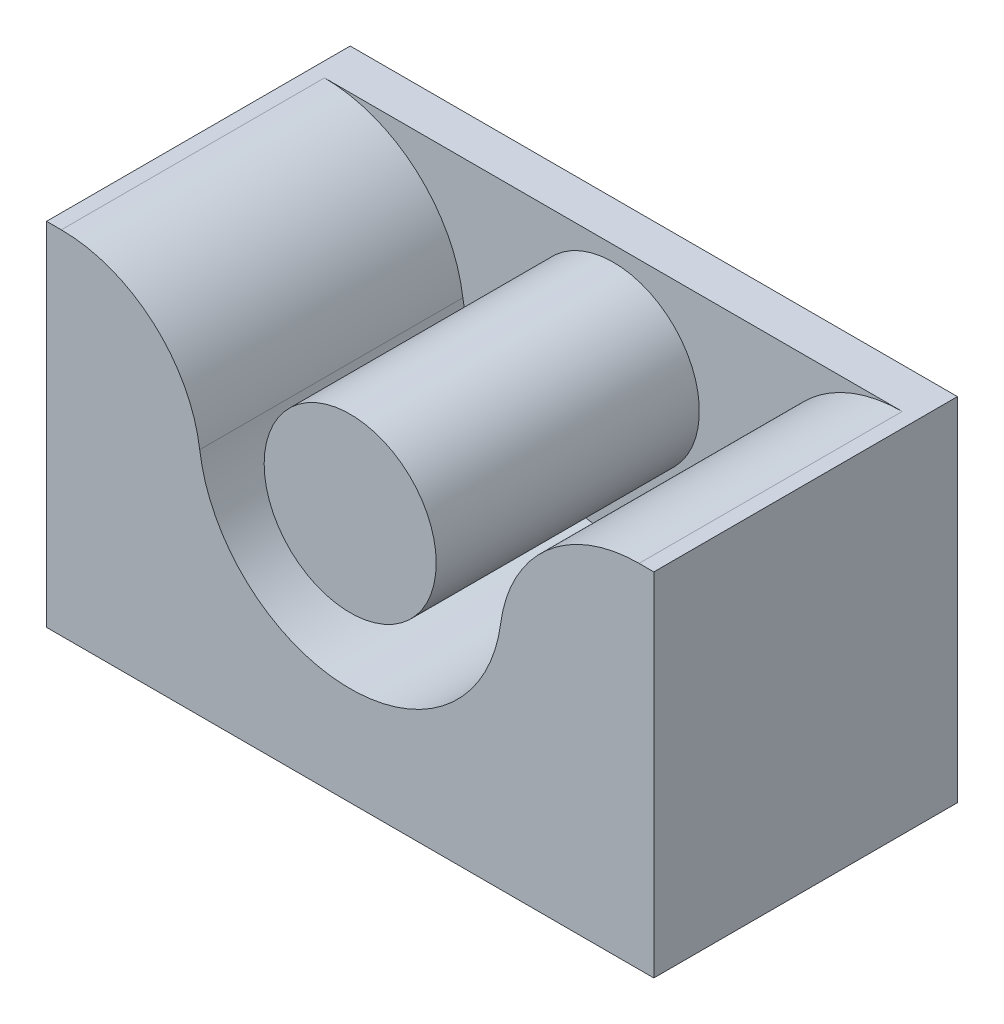
SolidWorks part; units mm, degrees
ref_plane "Alzado" through (0, 0, 0) normal (0, 0, 1) x (1, 0, 0)
ref_plane "Planta" through (0, 0, 0) normal (0, 1, 0) x (1, 0, 0)
ref_plane "Vista lateral" through (0, 0, 0) normal (1, 0, 0) x (0, 0, -1)
sketch "Croquis2" plane through (0, 0, 0) normal (0, 0, 1) x (1, 0, 0)
  line L0 (-15, 5) -> (15, 5)
  line L1 (-15, 5) -> (-15, -12.375)
  line L2 (-15, -12.375) -> (15, -12.375)
  line L3 (15, -12.375) -> (15, 5)
  dimension "D4" = 30
  dimension "D5" = 30
  dimension "D6" = 90
  dimension "D7" = 90
extrude "Saliente-Extruir1" add sketch "Croquis2" along normal blind 2
sketch "Croquis3" plane through (0, 0, 2) normal (0, 0, 1) x (1, 0, 0)
  line L0 (15, 5) -> (-15, 5) construction
  line L1 (-15, 5) -> (-14.2713, 5)
  line L2 (-15, 5) -> (-15, -12.375)
  line L3 (-15, -12.375) -> (15, -12.375)
  line L4 (15, 5) -> (15, -12.375)
  line L5 (14.2713, 5) -> (15, 5)
  line L6 (0, 6.4136) -> (0, 0) construction
  circle A0 centre (0, 0) radius 4.25
  arc A1 (-7.4346, -0.9881) -> (7.4346, -0.9881) centre (0, 0) ccw
  arc A2 (7.4346, -0.9881) -> (14.2713, 5) centre (14.2713, -1.8968) cw
  arc A3 (-7.4346, -0.9881) -> (-14.2713, 5) centre (-14.2713, -1.8968) ccw
  dimension "D1" = 15
  dimension "D2" = 8.5
  dimension "D3" = 30
extrude "Saliente-Extruir2" add sketch "Croquis3" along normal blind 13
sketch "Croquis4" plane through (0, -12.375, 0) normal (0, -1, 0) x (1, 0, 0)
  line L0 (-15, 0) -> (15, 0) construction
  circle A0 centre (-7, 7.5) radius 5
  circle A2 centre (7, 7.5) radius 5
  dimension "D1" = 10
  dimension "D2" = 10
  dimension "D3" = 7.5
  dimension "D4" = 7.5
  dimension "D5" = 7
  dimension "D6" = 7
extrude "Cortar-Extruir1" cut sketch "Croquis4" against normal blind 4.6
